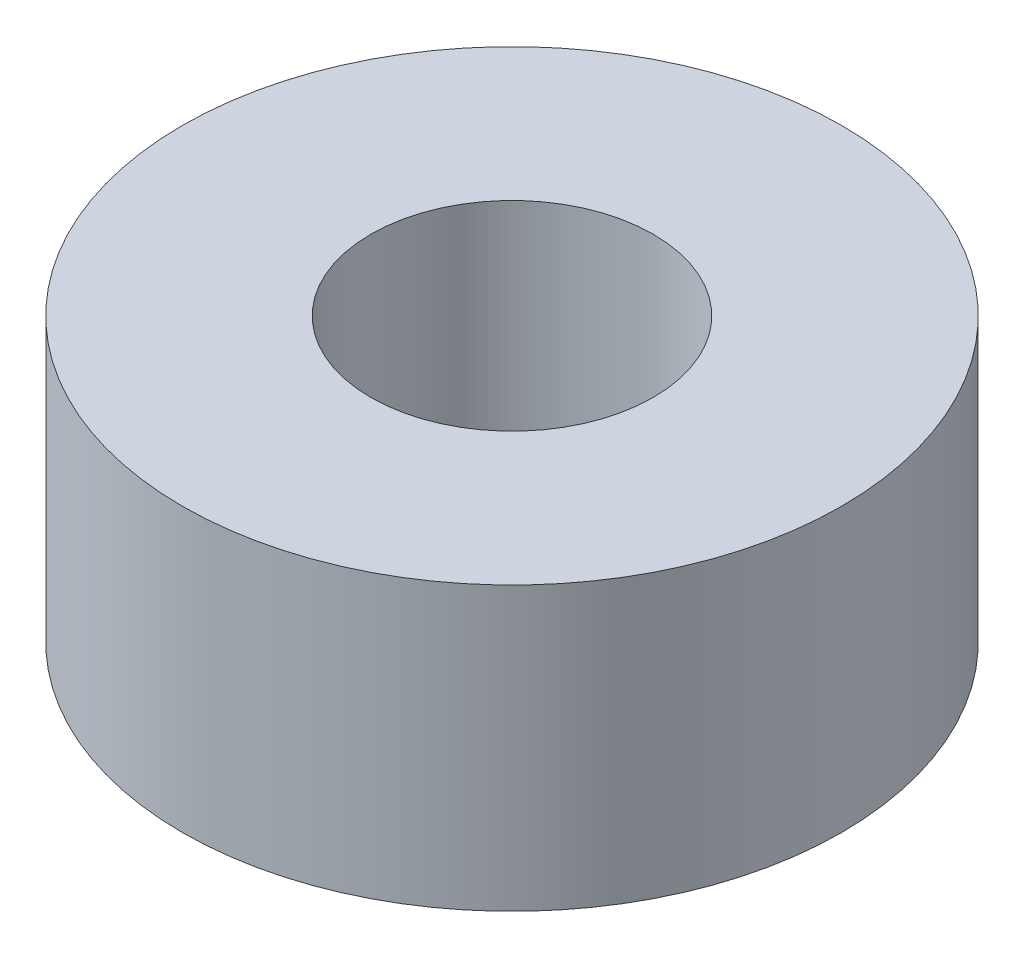
SolidWorks part; units mm, degrees
ref_plane "Front Plane" through (0, 0, 0) normal (0, 0, 1) x (1, 0, 0)
ref_plane "Top Plane" through (0, 0, 0) normal (0, 1, 0) x (1, 0, 0)
ref_plane "Right Plane" through (0, 0, 0) normal (1, 0, 0) x (0, 0, -1)
sketch "Sketch1" plane through (0, 0, 0) normal (0, 1, 0) x (1, 0, 0)
  circle A0 centre (0, 0) radius 4.7625
  circle A1 centre (0, 0) radius 11.1125
  dimension "D1" = 9.525
  dimension "D2" = 22.225
extrude "Boss-Extrude1" add sketch "Sketch1" along normal blind 9.525
